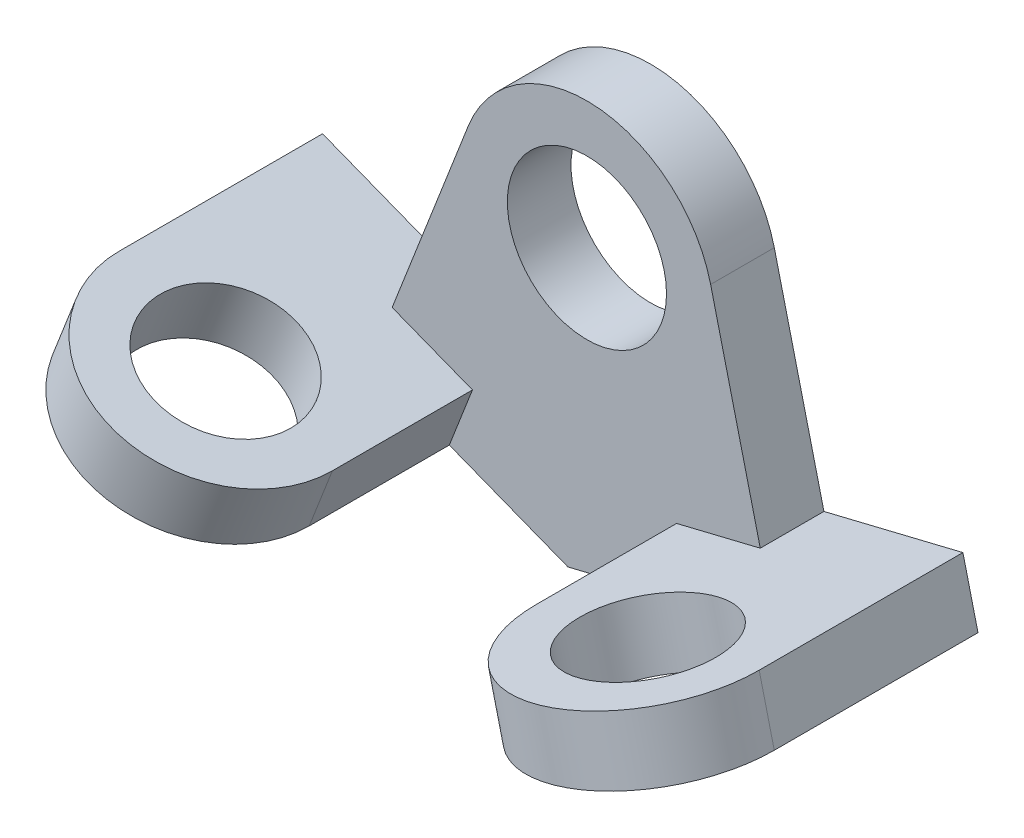
SolidWorks part; units mm, degrees
ref_plane "Front Plane" through (0, 0, 0) normal (0, 0, 1) x (1, 0, 0)
ref_plane "Top Plane" through (0, 0, 0) normal (0, 1, 0) x (1, 0, 0)
ref_plane "Right Plane" through (0, 0, 0) normal (1, 0, 0) x (0, 0, -1)
sketch "Sketch1" plane through (0, 0, 0) normal (0, 0, 1) x (1, 0, 0)
  line L0 (-34.2221, -32.7222) -> (-18.6342, 7.2642)
  line L1 (19.4308, 4.7377) -> (29.5971, -36.9581)
  line L3 (-2.9803, -44.9012) -> (-34.2221, -32.7222)
  line L4 (-2.9803, -44.9012) -> (29.5971, -36.9581)
  circle A0 centre (0, 0) radius 20
  circle A1 centre (0, 0) radius 12.5
  dimension "D1" = 40
  dimension "D5" = 25
  dimension "D2" = 35
  dimension "D3" = 45
extrude "Boss-Extrude1" add sketch "Sketch1" along normal blind 10 contours A0 L0 L3 L4 L1 | A0 A1
sketch "Sketch2" plane through (0, 0, 10) normal (0, 0, 1) x (1, 0, 0)
  line L0 (29.5971, -36.9581) -> (16.4505, -40.1635)
  line L1 (-2.9803, -44.9012) -> (29.5971, -36.9581) construction
  line L2 (16.4505, -40.1635) -> (14.0817, -30.4482)
  line L3 (14.0817, -30.4482) -> (49.0571, -21.9204)
  line L4 (49.0571, -21.9204) -> (51.4259, -31.6358)
  line L5 (51.4259, -31.6358) -> (16.4505, -40.1635)
  line L6 (-2.9803, -44.9012) -> (-8.3459, -42.8095)
  line L7 (-2.9803, -44.9012) -> (-34.2221, -32.7222) construction
  line M5 (29.5971, -36.9581) -> (19.4308, 4.7377)
  line M9 (-2.9803, -44.9012) -> (29.5971, -36.9581)
  dimension "D1" = 20
  dimension "D2" = 36
  dimension "D3" = 10
extrude "Boss-Extrude2" add sketch "Sketch2" along normal blind 64 contours L5 L4 L3 M5 | L3 L2 M9 M5
sketch "Sketch3" plane through (7.7975, -31.9804, 0) normal (-0.2369, 0.9715, 0) x (0.9715, 0.2369, 0)
  line L0 (20, -10) -> (42.4682, -10) construction
  line L1 (42.4682, -74) -> (42.4682, -10) construction
  line L2 (6.4682, -10) -> (6.4682, -32)
  line L3 (6.4682, -10) -> (42.4682, -10)
  line L4 (42.4682, -10) -> (42.4682, -32)
  line L5 (6.4682, -32) -> (6.4682, -74)
  line L6 (6.4682, -74) -> (6.4682, -10) construction
  line L7 (6.4682, -74) -> (42.4682, -74)
  line L8 (42.4682, -74) -> (42.4682, -32)
  arc A0 (6.4682, -32) -> (42.4682, -32) centre (24.4682, -32) ccw
  circle A1 centre (24.4682, -32) radius 11
  line M7 (6.4682, -10) -> (6.4682, -74)
  line M8 (6.4682, -74) -> (42.4682, -74)
  line M9 (42.4682, -74) -> (42.4682, -10)
  dimension "D3" = 36
  dimension "D4" = 22
  dimension "D1" = 22
  dimension "D2" = 18
extrude "Cut-Extrude1" cut sketch "Sketch3" against normal blind 64 contours A1 | A0 M7 M8 M9
sketch "Sketch4" plane through (0, 0, 10) normal (0, 0, 1) x (1, 0, 0)
  line L0 (0, 0) -> (-2.9803, -44.9012) construction
ref_plane "Plane1" through (0, 0, 0) normal (-0.9978, 0.0662, 0) x (-0.0662, -0.9978, 0)
mirror "Mirror1" about plane through (0, 0, 0) normal (-0.9978, 0.0662, 0) of "Cut-Extrude1", "Boss-Extrude2"
sketch "Sketch5" plane through (0, 0, 10) normal (0, 0, -1) x (-1, 0, 0)
  line L0 (-49.0571, -21.9204) -> (-51.4259, -31.6358)
  line L1 (-51.4259, -31.6358) -> (-29.5971, -36.9581)
  line L2 (-29.5971, -36.9581) -> (-27.2283, -27.2427)
  line L3 (-27.2283, -27.2427) -> (-49.0571, -21.9204)
extrude "Boss-Extrude3" add sketch "Sketch5" along normal blind 10
sketch "Sketch6" plane through (0, 0, 10) normal (0, 0, -1) x (-1, 0, 0)
  line L0 (30.59, -23.4051) -> (34.2221, -32.7222)
  line L1 (55.1559, -24.5615) -> (34.2221, -32.7222) construction
  line L2 (34.2221, -32.7222) -> (30.59, -23.4051) construction
  line L3 (34.2221, -32.7222) -> (55.1559, -24.5615)
  line L4 (55.1559, -24.5615) -> (51.5238, -15.2445)
  line L5 (51.5238, -15.2445) -> (30.59, -23.4051)
extrude "Boss-Extrude4" add sketch "Sketch6" along normal blind 10
